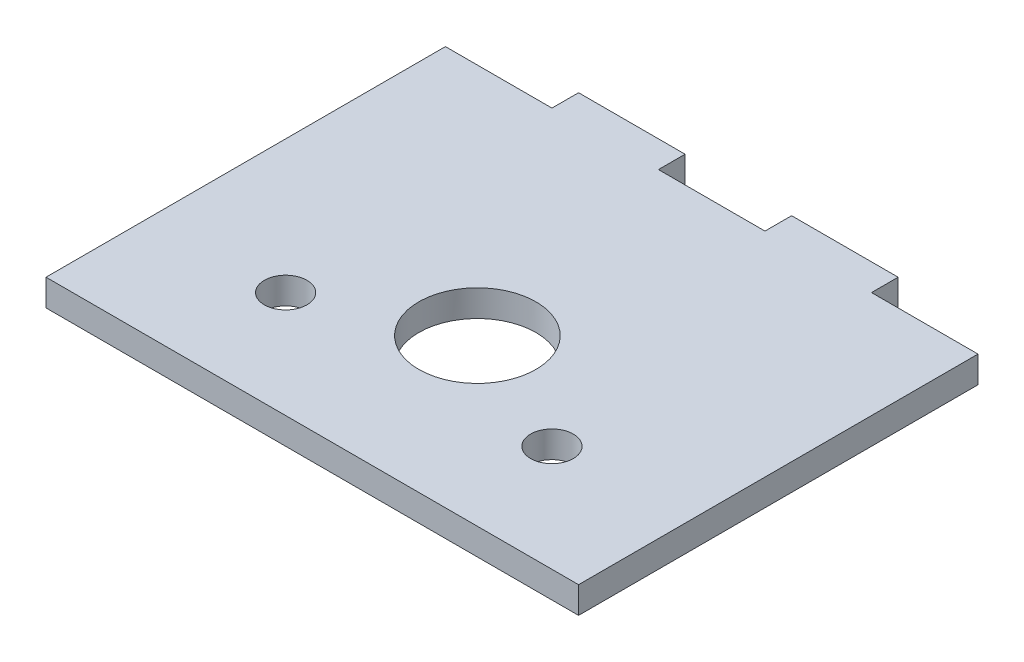
SolidWorks part; units mm, degrees
material "Acrylic (Medium-high impact)"
ref_plane "Front Plane" through (0, 0, 0) normal (0, 0, 1) x (1, 0, 0)
ref_plane "Top Plane" through (0, 0, 0) normal (0, 1, 0) x (1, 0, 0)
ref_plane "Right Plane" through (0, 0, 0) normal (1, 0, 0) x (0, 0, -1)
sketch "Sketch1" plane through (0, 0, 0) normal (0, 1, 0) x (1, 0, 0)
  line L0 (-1000, 0) -> (49000, 0) construction
  line L5 (0, -1000) -> (0, 49000) construction
  line L6 (-50, 44) -> (-30, 44)
  line L7 (-50, -31) -> (50, -31)
  line L8 (-50, -31) -> (-50, 44)
  line L9 (-30, 49) -> (-10, 49)
  line L10 (50, -31) -> (50, 44)
  line L11 (-30, 49) -> (-30, 44)
  line L12 (-10, 49) -> (-10, 44)
  line L13 (10, 49) -> (10, 44)
  line L14 (30, 49) -> (30, 44)
  line L16 (30, 44) -> (50, 44)
  line L17 (10, 49) -> (30, 49)
  line L18 (-10, 44) -> (10, 44)
  circle A10 centre (0, 0) radius 4
  circle A15 centre (25, -11) radius 4
  circle A16 centre (-25, -11) radius 4
  point P6 (0, 44)
  dimension "D3" = 8
  dimension "D4" = 20
  dimension "D12" = 8
  dimension "D2" = 100
  dimension "D5" = 31
  dimension "D7" = 5
  dimension "D9" = 4
  dimension "D8" = 20
  dimension "D10" = 20
  dimension "D11" = 80
  dimension "D13" = 25
extrude "Boss-Extrude1" add sketch "Sketch1" along normal blind 5
sketch "Sketch2" plane through (0, 5, 0) normal (0, 1, 0) x (1, 0, 0)
  circle A0 centre (0, 0) radius 11
  dimension "D1" = 22
extrude "Cut-Extrude1" cut sketch "Sketch2" against normal up to next
